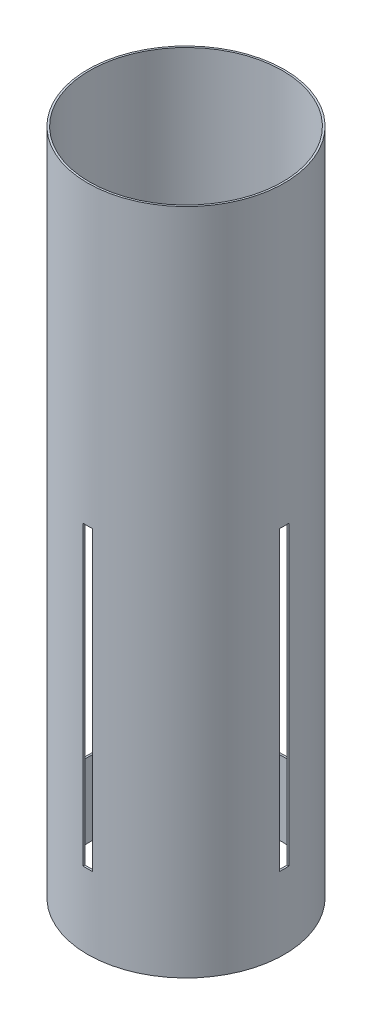
SolidWorks part; units mm, degrees
material "Thornel Mat VMA"
ref_plane "Front Plane" through (0, 0, 0) normal (0, 0, 1) x (1, 0, 0)
ref_plane "Top Plane" through (0, 0, 0) normal (0, 1, 0) x (1, 0, 0)
ref_plane "Right Plane" through (0, 0, 0) normal (1, 0, 0) x (0, 0, -1)
sketch "Sketch1" plane through (0, 0, 0) normal (0, 1, 0) x (1, 0, 0)
  circle A0 centre (0, 0) radius 66.04
  circle A1 centre (0, 0) radius 67.31
  dimension "D1" = 132.08
  dimension "D2" = 1.27
extrude "Boss-Extrude1" add sketch "Sketch1" along normal blind 457.2
sketch "Sketch3" plane through (0, 0, 0) normal (0, 0, 1) x (1, 0, 0)
  line L0 (3.175, 50.8) -> (-3.175, 50.8)
  line L1 (3.175, 0) -> (-3.175, 0)
  line L2 (3.175, 0) -> (3.175, 254)
  line L3 (3.175, 254) -> (-3.175, 254)
  line L4 (-3.175, 0) -> (-3.175, 254)
  dimension "D1" = 254
  dimension "D2" = 6.35
  dimension "D3" = 50.8
extrude "Cut-Extrude1" cut sketch "Sketch3" against normal through all both and the other way through all contours L4 L0 L2 L3
pattern_circular "CirPattern1" count 4 over 360 about axis through (0, 0, 0) along (0, 1, 0) of "Cut-Extrude1"
